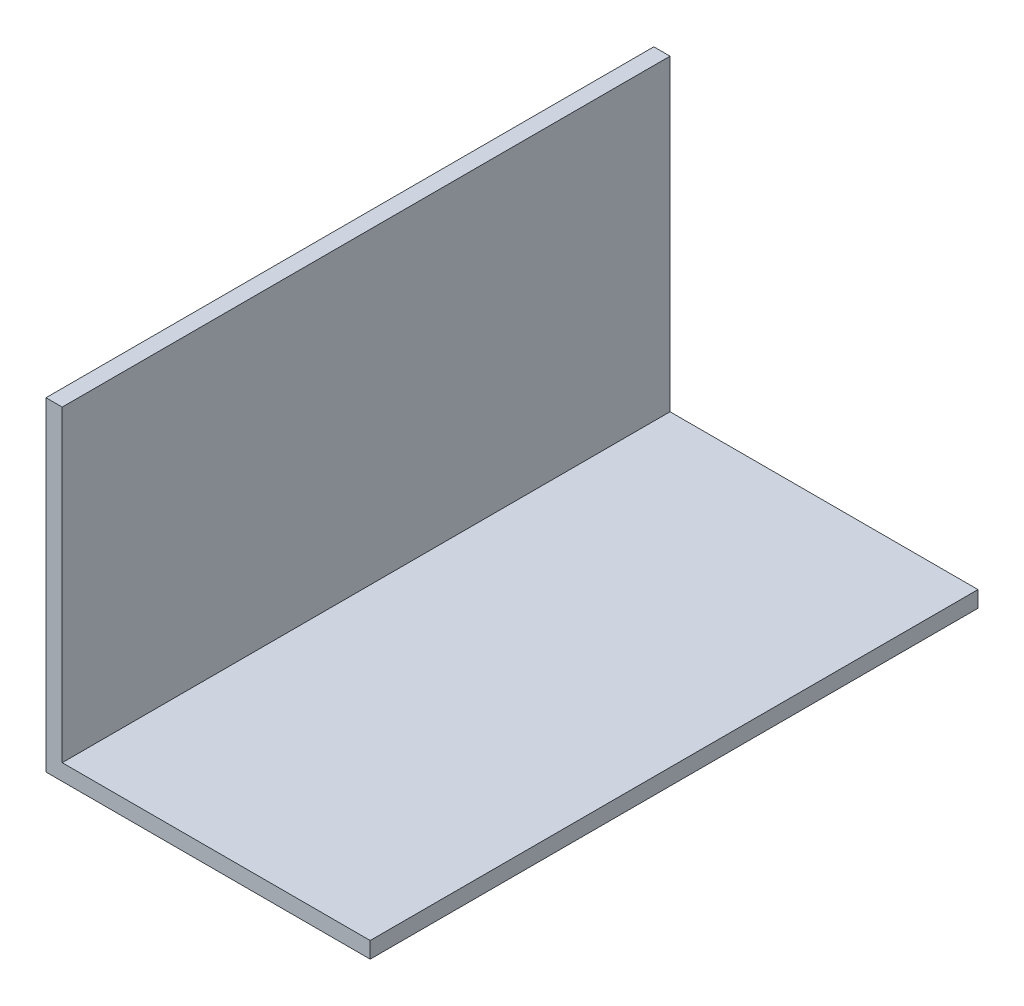
SolidWorks part; units mm, degrees
ref_plane "Płaszczyzna przednia" through (0, 0, 0) normal (0, 0, 1) x (1, 0, 0)
ref_plane "Płaszczyzna górna" through (0, 0, 0) normal (0, 1, 0) x (1, 0, 0)
ref_plane "Płaszczyzna prawa" through (0, 0, 0) normal (1, 0, 0) x (0, 0, -1)
sketch "Sketch1" plane through (0, 0, 0) normal (0, 0, 1) x (1, 0, 0)
  line L1 (-2, 40) -> (2, 40)
  line L2 (-2, 40) -> (-2, -40)
  line L3 (-2, -40) -> (2, -40)
  line L4 (2, 40) -> (2, -40)
  line L5 (-2, 40) -> (2, -40) construction
  line L6 (-2, -40) -> (2, 40) construction
  line L7 (-2, -40) -> (78, -40)
  line L8 (-2, -40) -> (-2, -36)
  line L9 (-2, -36) -> (78, -36)
  line L10 (78, -40) -> (78, -36)
  line L11 (-2, -40) -> (78, -36) construction
  line L12 (-2, -36) -> (78, -40) construction
  point P0 (0, 0)
  point P9 (38, -38)
  dimension "D1" = 80
  dimension "D2" = 4
  dimension "D3" = 80
  dimension "D4" = 4
extrude "Boss-Extrude1" add sketch "Sketch1" along normal blind 150 contours L2 L9 L4 L1 | L9 L2 L3 L4 | L7 L10 L9 L4
